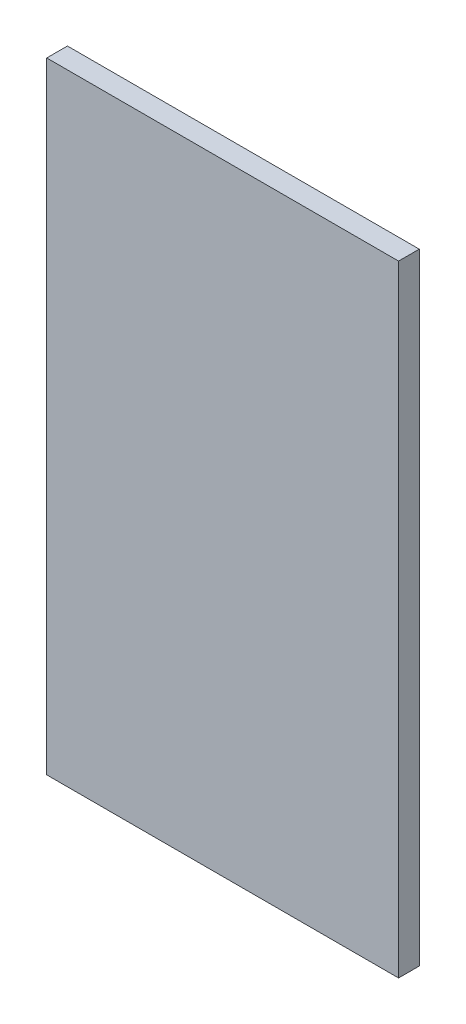
SolidWorks part; units mm, degrees
ref_plane "前视基准面" through (0, 0, 0) normal (0, 0, 1) x (1, 0, 0)
ref_plane "上视基准面" through (0, 0, 0) normal (0, 1, 0) x (1, 0, 0)
ref_plane "右视基准面" through (0, 0, 0) normal (1, 0, 0) x (0, 0, -1)
sketch "草图1" plane through (0, 0, 0) normal (0, 0, 1) x (1, 0, 0)
  line L0 (-56.5826, 23.7372) -> (-56.5826, -276.2628)
  line L1 (-56.5826, -276.2628) -> (113.4174, -276.2628)
  line L2 (113.4174, -276.2628) -> (113.4174, 23.7372)
  line L3 (113.4174, 23.7372) -> (-56.5826, 23.7372)
  dimension "D1" = 300
  dimension "D2" = 170
extrude "凸台-拉伸1" add sketch "草图1" along normal blind 10
